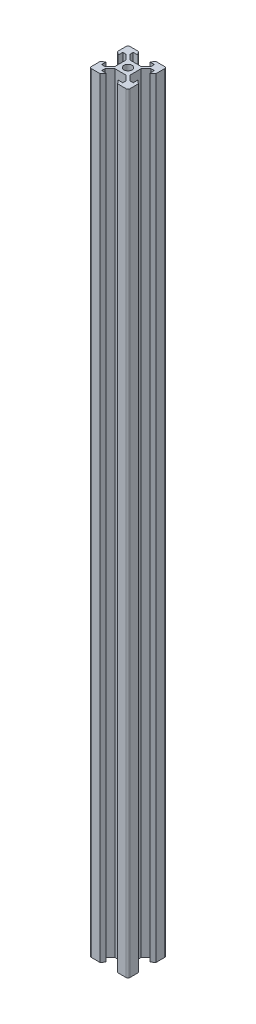
SolidWorks part; units mm, degrees
ref_plane "Front Plane" through (0, 0, 0) normal (0, 0, 1) x (1, 0, 0)
ref_plane "Top Plane" through (0, 0, 0) normal (0, 1, 0) x (1, 0, 0)
ref_plane "Right Plane" through (0, 0, 0) normal (1, 0, 0) x (0, 0, -1)
sketch "Sketch1" plane through (0, 0, 0) normal (0, 1, 0) x (1, 0, 0)
  line L0 (-3.125, 8.2) -> (-4.58, 10)
  line L1 (-9, 10) -> (9, 10)
  line L2 (-10, 9) -> (-10, -9)
  line L3 (-9, -10) -> (9, -10)
  line L4 (10, 9) -> (10, -9)
  line L5 (-10, 10) -> (10, -10) construction
  line L6 (-10, -10) -> (10, 10) construction
  line L7 (-10, 0) -> (0, 0) construction
  line L8 (0, 10) -> (0, 0) construction
  line L9 (-8.2, 3.125) -> (-10, 4.58)
  line L10 (-8.2, 3.125) -> (-8.2, 5.5)
  line L11 (-3.125, 8.2) -> (-5.5, 8.2)
  line L12 (-5.5, 8.2) -> (-5.5, 6.56)
  line L13 (-2.84, 3.9) -> (2.84, 3.9)
  line L14 (-5.5, 6.56) -> (-2.84, 3.9)
  line L15 (-8.2, 5.5) -> (-6.56, 5.5)
  line L16 (-6.56, 5.5) -> (-3.9, 2.84)
  line L17 (-3.9, 2.84) -> (-3.9, -2.84)
  line L18 (3.9, 2.84) -> (3.9, -2.84)
  line L19 (6.56, 5.5) -> (3.9, 2.84)
  line L20 (8.2, 5.5) -> (6.56, 5.5)
  line L21 (8.2, 3.125) -> (8.2, 5.5)
  line L22 (8.2, 3.125) -> (10, 4.58)
  line L23 (3.125, 8.2) -> (4.58, 10)
  line L24 (3.125, 8.2) -> (5.5, 8.2)
  line L25 (5.5, 8.2) -> (5.5, 6.56)
  line L26 (5.5, 6.56) -> (2.84, 3.9)
  line L27 (-8.2, -3.125) -> (-10, -4.58)
  line L28 (-8.2, -3.125) -> (-8.2, -5.5)
  line L29 (-8.2, -5.5) -> (-6.56, -5.5)
  line L30 (-6.56, -5.5) -> (-3.9, -2.84)
  line L31 (8.2, -3.125) -> (10, -4.58)
  line L32 (8.2, -3.125) -> (8.2, -5.5)
  line L33 (8.2, -5.5) -> (6.56, -5.5)
  line L34 (6.56, -5.5) -> (3.9, -2.84)
  line L35 (5.5, -6.56) -> (2.84, -3.9)
  line L36 (5.5, -8.2) -> (5.5, -6.56)
  line L37 (3.125, -8.2) -> (5.5, -8.2)
  line L38 (3.125, -8.2) -> (4.58, -10)
  line L39 (-5.5, -6.56) -> (-2.84, -3.9)
  line L40 (-2.84, -3.9) -> (2.84, -3.9)
  line L41 (-5.5, -8.2) -> (-5.5, -6.56)
  line L42 (-3.125, -8.2) -> (-5.5, -8.2)
  line L43 (-3.125, -8.2) -> (-4.58, -10)
  circle A0 centre (0, 0) radius 2.1
  arc A1 (-10, -9) -> (-9, -10) centre (-9, -9) ccw
  arc A2 (9, -10) -> (10, -9) centre (9, -9) ccw
  arc A3 (9, 10) -> (10, 9) centre (9, 9) cw
  arc A4 (-9, 10) -> (-10, 9) centre (-9, 9) ccw
  point P0 (0, 0)
  point P35 (0, 3.9)
  point P40 (-3.9, 0)
  point P41 (3.9, 0)
  dimension "D3" = 4.2
  dimension "D2" = 1
  dimension "D1" = 20
  dimension "D4" = 6.1
  dimension "D5" = 6.25
  dimension "D6" = 11
  dimension "D7" = 5.68
  dimension "D8" = 9.16
  dimension "D9" = 1.8
extrude "Boss-Extrude1" add sketch "Sketch1" along normal blind 400 contours L43 L42 L41 L39 L40 L35 L36 L37 L38 L3 L4 L31 L32 L33 L34 L18 L19 L20 L21 L22 L1 L23 L24 L25 L26 L13 L14 L12 L11 L0 L2 L9 L10 L15 L16 L17 L30 L29 L28 L27 A0
